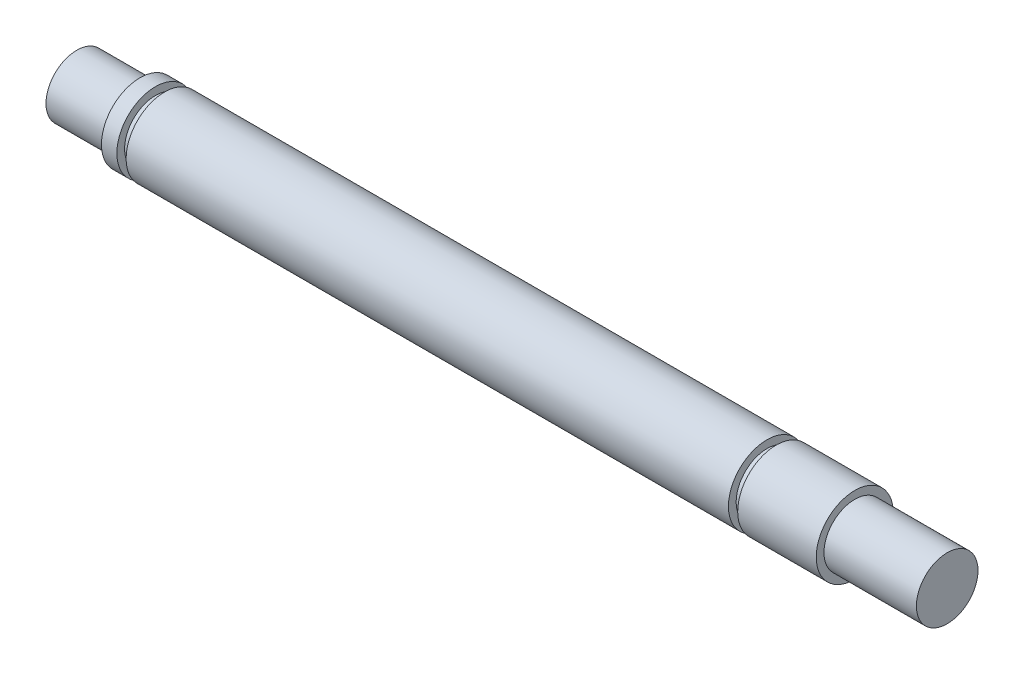
SolidWorks part; units mm, degrees
material "AISI 1020 Steel, Cold Rolled"
ref_plane "Front" through (0, 0, 0) normal (0, 0, 1) x (1, 0, 0)
ref_plane "Top" through (0, 0, 0) normal (0, 1, 0) x (1, 0, 0)
ref_plane "Right" through (0, 0, 0) normal (1, 0, 0) x (0, 0, -1)
sketch "Sketch1" plane through (0, 0, 0) normal (0, 0, 1) x (1, 0, 0)
  line L0 (0, 0) -> (23127.3115, 0) construction
  line L1 (0, 0) -> (0, -23127.3115) construction
  line L2 (-39.2, -5) -> (39, -5)
  line L3 (39, -5) -> (39, -4)
  line L4 (-39.2, -5) -> (-39.2, -4)
  line L5 (39, -4) -> (40.2, -4)
  line L6 (-39.2, -4) -> (-40.4, -4)
  line L7 (40.2, -4) -> (40.2, -5)
  line L9 (40.2, -5) -> (50.4, -5)
  line L10 (-42.4, -4) -> (-50.6, -4)
  line L11 (50.4, -5) -> (50.4, 0)
  line L12 (-50.6, -4) -> (-50.6, 0)
  line L13 (50.4, 0) -> (-50.6, 0)
  line L15 (-40.4, -4) -> (-40.4, -5)
  line L16 (-40.4, -5) -> (-42.4, -5)
  line L17 (-42.4, -5) -> (-42.4, -4)
  point P8 (0, -5)
  point P18 (44.4, -5)
  point P19 (-46.6, -4)
  dimension "D1" = 1.2
  dimension "D2" = 101
  dimension "D3" = 39
  dimension "D4" = 5
  dimension "D5" = 4
  dimension "D6" = 5
  dimension "D7" = 4
  dimension "D8" = 4
  dimension "D9" = 6
  dimension "D10" = 39.2
  dimension "D11" = 4
  dimension "D12" = 1.2
  dimension "D13" = 50.4
  dimension "D14" = 2
revolve "Revolve1" add sketch "Sketch1" angle 360 about L0
ref_plane "Plane1" through (-0.1, 0, 0) normal (-1, 0, 0) x (0, 0, 1)
ref_plane "Plane2" through (0, -5, 0) normal (0, 1, 0) x (1, 0, 0)
hole_wizard "M4 Clearance Hole5" positions "3DSketch9" profile "Sketch16" hole size "M4" standard "ANSI Metric"
sketch3d "3DSketch9"
  point P0 (44.4, -5, 0)
  point P3 (44.4, -5, 0)
sketch "Sketch16" plane through (44.4, -5, 0) normal (1, 0, 0) x (0, 0, -1)
  line L0 (0, 0) -> (0, 6.4519)
  line L1 (0, 6.4519) -> (2.25, 5.1)
  line L2 (2.25, 5.1) -> (2.25, 0)
  line L5 (2.25, 0) -> (0, 0)
  line L10 (0, 6.4519) -> (-2.25, 5.1) construction
  line L11 (0, -6.35) -> (0, 107.95) construction
  dimension "Hole Dia." = 4.5
  dimension "Hole Depth" = 5.1
  dimension "Drill Angle" = 118
sketch "Sketch17" plane through (50.4, 0, 0) normal (1, 0, 0) x (0, 0, -1)
  circle A0 centre (0, 0) radius 4
  dimension "D1" = 8
extrude "Boss-Extrude1" add sketch "Sketch17" along normal blind 12
